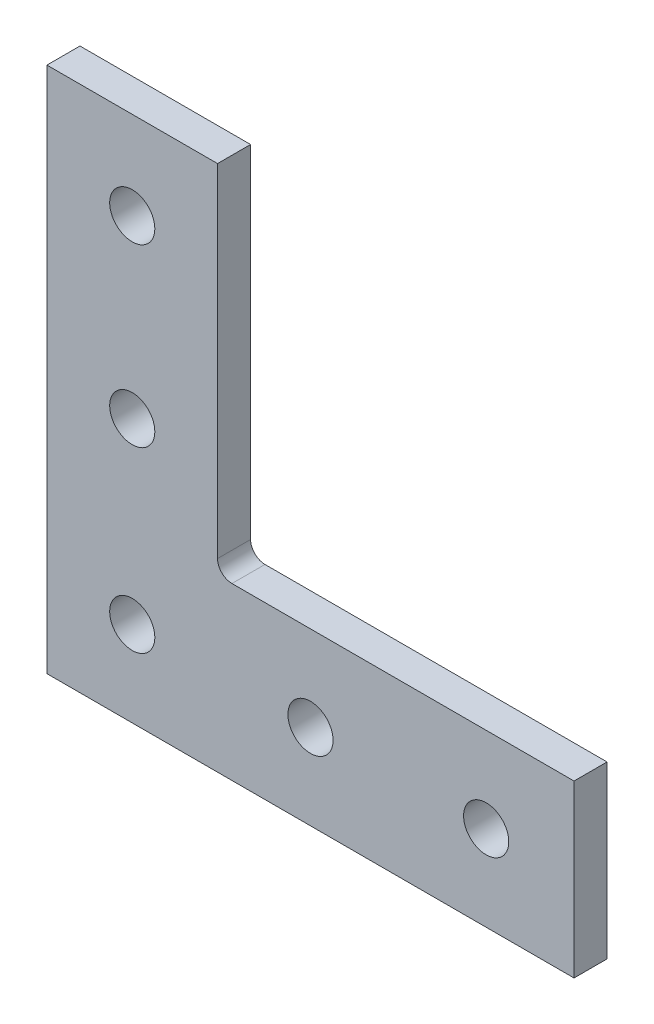
SolidWorks part; units mm, degrees
material "6061-T6 (SS)"
ref_plane "Front Plane" through (0, 0, 0) normal (0, 0, 1) x (1, 0, 0)
ref_plane "Top Plane" through (0, 0, 0) normal (0, 1, 0) x (1, 0, 0)
ref_plane "Right Plane" through (0, 0, 0) normal (1, 0, 0) x (0, 0, -1)
sketch "Sketch1" plane through (0, 0, 0) normal (0, 0, 1) x (1, 0, 0)
  line L0 (-38.1, -38.1) -> (-38.1, 38.1) construction
  line L1 (38.1, -38.1) -> (-38.1, -38.1) construction
  line L2 (-38.1, 38.1) -> (-13.4366, 38.1) construction
  line L3 (-29.0322, 25.4) -> (-22.5044, 25.4) construction
  point P0 (-25.7683, 38.1)
  point P3 (-25.7683, 0)
  point P4 (-38.1, 0)
  point P6 (-38.1, 38.1)
  point P8 (-38.1, 0)
  point P10 (0, 0)
  point P12 (0, -38.1)
  point P14 (-25.7683, 25.4)
  dimension "Length" = 76.2
  dimension "Width" = 24.6634
  dimension "Hole to Edge" = 12.7
  dimension "Hole Spacing" = 25.4
  dimension "Hole Dia" = 6.5278
sketch "Sketch2" plane through (0, 0, 0) normal (1, 0, 0) x (0, 0, -1)
  line L0 (2.3876, 0) -> (-2.3876, 0) construction
  point P4 (0, 0)
  dimension "Thickness" = 4.7752
sketch "Sketch3" plane through (0, 0, 0) normal (0, 0, 1) x (1, 0, 0)
  line L0 (-13.4366, 38.1) -> (-38.1, 38.1)
  line L1 (-38.1, 38.1) -> (-38.1, -38.1)
  line L2 (-38.1, -38.1) -> (38.1, -38.1)
  line L3 (38.1, -38.1) -> (38.1, -13.4366)
  line L4 (38.1, -13.4366) -> (-11.3538, -13.4366)
  line L5 (-13.4366, -11.3538) -> (-13.4366, 38.1)
  arc A0 (-11.3538, -13.4366) -> (-13.4366, -11.3538) centre (-11.3538, -11.3538) cw
  dimension "Radius" = 2.0828
extrude "Boss-Extrude1" add sketch "Sketch3" against normal up to vertex (2.3876 mm away) and the other way up to vertex (2.3876 mm away) up to point (0, 0, -2.3876) other way up to point (0, 0, 2.3876)
sketch "Sketch4" plane through (0, 0, 2.3876) normal (0, 0, 1) x (1, 0, 0)
  line L0 (-29.0322, 25.4) -> (-22.5044, 25.4) construction
  line L1 (-38.1, -38.1) -> (0, 0) construction
  circle A0 centre (-25.7683, 25.4) radius 3.2639
  circle A1 centre (-25.7683, 0) radius 3.2639
  circle A3 centre (0, -25.7683) radius 3.2639
  circle A4 centre (25.4, -25.7683) radius 3.2639
  circle A5 centre (-25.7683, -25.7683) radius 3.2639
extrude "Cut-Extrude1" cut sketch "Sketch4" against normal through all both and the other way through all
